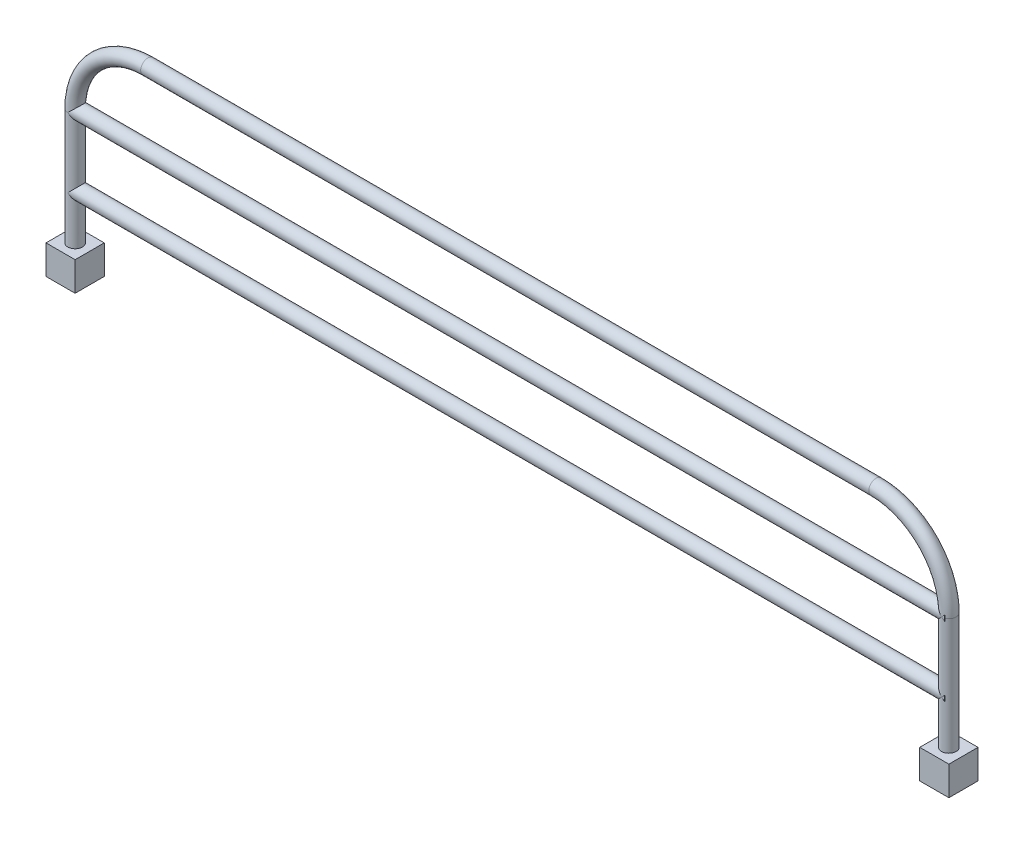
SolidWorks part; units mm, degrees
ref_plane "Front Plane" through (0, 0, 0) normal (0, 0, 1) x (1, 0, 0)
ref_plane "Top Plane" through (0, 0, 0) normal (0, 1, 0) x (1, 0, 0)
ref_plane "Right Plane" through (0, 0, 0) normal (1, 0, 0) x (0, 0, -1)
sketch "Sketch1" plane through (0, 0, 0) normal (0, 0, 1) x (1, 0, 0)
  line L0 (0, 0) -> (0, 203.2)
  line L1 (1524, 203.2) -> (1524, 0)
  line L3 (127, 330.2) -> (1397, 330.2)
  arc A0 (1397, 330.2) -> (1524, 203.2) centre (1397, 203.2) cw
  arc A1 (0, 203.2) -> (127, 330.2) centre (127, 203.2) cw
  dimension "D1" = 127
  dimension "D2" = 1524
  dimension "D3" = 203.2
sketch "Sketch2" plane through (0, 0, 0) normal (0, 1, 0) x (1, 0, 0)
  circle A0 centre (0, 0) radius 12.7
  dimension "D1" = 25.4
sweep "Sweep1" add profiles "Sketch2" path "Sketch1"
sketch "Sketch3" plane through (0, 0, 0) normal (0, -1, 0) x (1, 0, 0)
  line L1 (25.4, 25.4) -> (-25.4, 25.4)
  line L2 (25.4, 25.4) -> (25.4, -25.4)
  line L3 (25.4, -25.4) -> (-25.4, -25.4)
  line L4 (-25.4, 25.4) -> (-25.4, -25.4)
  line L5 (25.4, 25.4) -> (-25.4, -25.4) construction
  line L6 (25.4, -25.4) -> (-25.4, 25.4) construction
  line L7 (1549.4, 25.4) -> (1498.6, 25.4)
  line L8 (1549.4, 25.4) -> (1549.4, -25.4)
  line L9 (1549.4, -25.4) -> (1498.6, -25.4)
  line L10 (1498.6, 25.4) -> (1498.6, -25.4)
  line L11 (1549.4, 25.4) -> (1498.6, -25.4) construction
  line L12 (1549.4, -25.4) -> (1498.6, 25.4) construction
  point P0 (0, 0)
  point P6 (1524, 0)
  dimension "D1" = 50.8
  dimension "D2" = 50.8
  dimension "D3" = 50.8
  dimension "D4" = 50.8
extrude "Boss-Extrude1" add sketch "Sketch3" along normal blind 50.8
sketch "Sketch4" plane through (0, 0, 0) normal (1, 0, 0) x (0, 0, -1)
  line L0 (-12.7, 203.2) -> (12.7, 203.2) construction
  circle A0 centre (0, 203.2) radius 12.7
  dimension "D1" = 25.4
extrude "Boss-Extrude2" add sketch "Sketch4" along normal blind 1528.8
sketch "Sketch5" plane through (0, 0, 0) normal (1, 0, 0) x (0, 0, -1)
  circle A0 centre (0, 82.0991) radius 12.7
  dimension "D1" = 25.4
extrude "Boss-Extrude3" add sketch "Sketch5" along normal blind 1528.8
